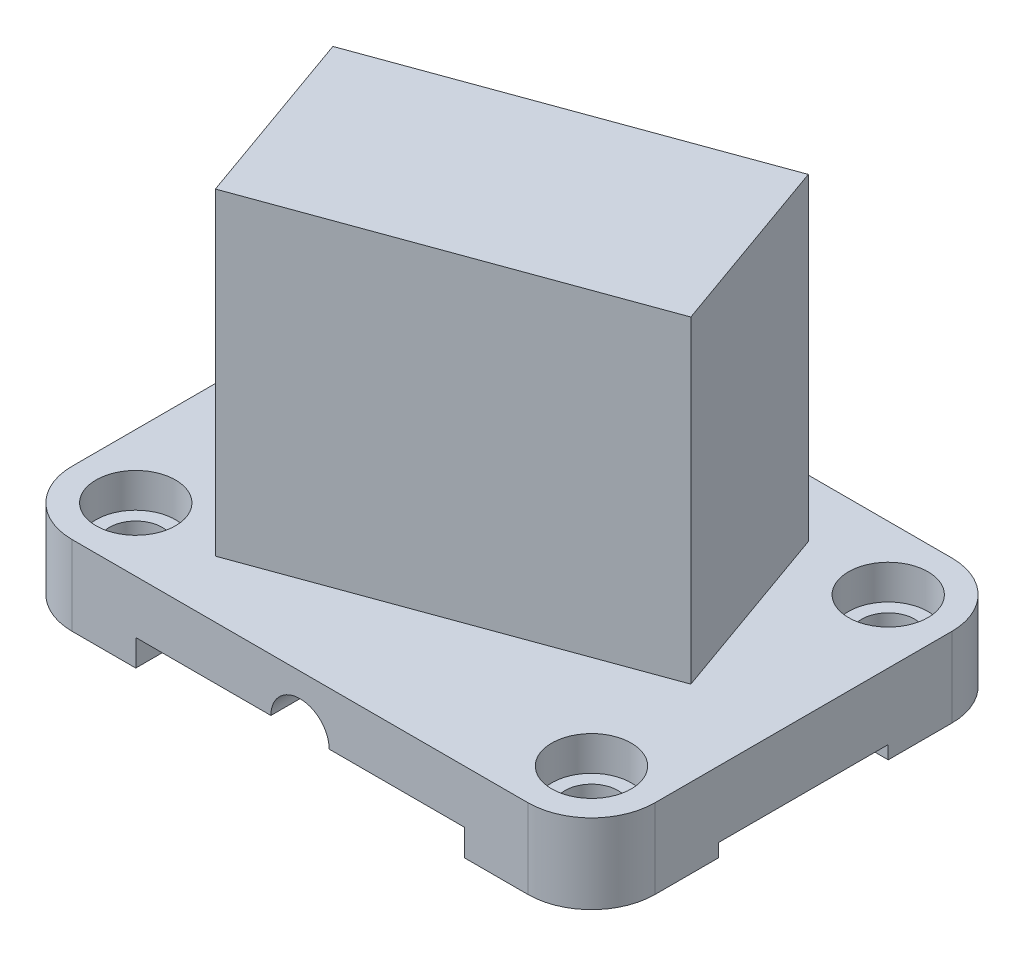
SolidWorks part; units mm, degrees
ref_plane "Front Plane" through (0, 0, 0) normal (0, 0, 1) x (1, 0, 0)
ref_plane "Top Plane" through (0, 0, 0) normal (0, 1, 0) x (1, 0, 0)
ref_plane "Right Plane" through (0, 0, 0) normal (1, 0, 0) x (0, 0, -1)
sketch "Sketch1" plane through (0, 0, 0) normal (0, 1, 0) x (1, 0, 0)
  line L1 (-54.61, 50.8) -> (54.61, 50.8)
  line L2 (-69.85, 35.56) -> (-69.85, -35.56)
  line L3 (-54.61, -50.8) -> (54.61, -50.8)
  line L4 (69.85, 35.56) -> (69.85, -35.56)
  line L5 (-69.85, 50.8) -> (69.85, -50.8) construction
  line L6 (-69.85, -50.8) -> (69.85, 50.8) construction
  arc A0 (-54.61, 50.8) -> (-69.85, 35.56) centre (-54.61, 35.56) ccw
  arc A1 (54.61, 50.8) -> (69.85, 35.56) centre (54.61, 35.56) cw
  arc A2 (54.61, -50.8) -> (69.85, -35.56) centre (54.61, -35.56) ccw
  arc A3 (-69.85, -35.56) -> (-54.61, -50.8) centre (-54.61, -35.56) ccw
  point P0 (0, 0)
  dimension "D3" = 15.24
  dimension "D1" = 139.7
  dimension "D2" = 101.6
extrude "Boss-Extrude1" add sketch "Sketch1" along normal blind 19.05
sketch "Sketch2" plane through (0, 19.05, 0) normal (0, 1, 0) x (1, 0, 0)
  point P0 (-54.61, 35.56)
  point P1 (54.61, 35.56)
  point P3 (-54.61, -35.56)
  point P5 (54.61, -35.56)
hole_wizard "CBORE for 1/2 Hex Head Bolt1" positions "Sketch2" profile "Sketch3" counterbore size "1/2" standard "ANSI Inch" end condition up to next
sketch "Sketch3" plane through (-54.61, 19.05, -35.56) normal (1, 0, 0) x (0, 0, 1)
  line L0 (0, 0) -> (0, 19.05)
  line L1 (0, 19.05) -> (6.35, 19.05)
  line L3 (6.35, 19.05) -> (6.35, 8.255)
  line L4 (6.35, 8.255) -> (9.525, 8.255)
  line L5 (9.525, 8.255) -> (9.525, 0)
  line L7 (9.525, 0) -> (0, 0)
  line L11 (0, -6.35) -> (0, 107.95) construction
  dimension "Thru Hole Dia." = 12.7
  dimension "Thru Hole Depth" = 19.05
  dimension "C'Bore Dia." = 19.05
  dimension "C'Bore Depth" = 8.255
sketch "Sketch4" plane through (0, 0, 50.8) normal (0, 0, 1) x (1, 0, 0)
  line L0 (-39.37, 0) -> (-39.37, 6.35)
  line L1 (-54.61, 0) -> (54.61, 0) construction
  line L2 (-39.37, 6.35) -> (-6.985, 6.35)
  line L3 (39.37, 6.35) -> (39.37, 0)
  line L4 (39.37, 0) -> (-39.37, 0)
  line L5 (-69.85, 19.05) -> (-69.85, 0) construction
  line L6 (6.985, 6.35) -> (39.37, 6.35)
  arc A0 (6.985, 6.35) -> (-6.985, 6.35) centre (0, 6.35) ccw
  dimension "D4" = 13.97
  dimension "D1" = 6.35
  dimension "D2" = 39.37
  dimension "D3" = 30.48
extrude "Cut-Extrude1" cut sketch "Sketch4" against normal through all
sketch "Sketch5" plane through (-69.85, 0, 0) normal (-1, 0, 0) x (0, 0, 1)
  line L0 (-20.32, 0) -> (-20.32, 3.175)
  line L1 (-35.56, 0) -> (35.56, 0) construction
  line L2 (-20.32, 3.175) -> (20.32, 3.175)
  line L3 (20.32, 3.175) -> (20.32, 0)
  line L4 (20.32, 0) -> (-20.32, 0)
  line L5 (-50.8, 19.05) -> (-50.8, 0) construction
  line L6 (50.8, 19.05) -> (50.8, 0) construction
  dimension "D1" = 30.48
  dimension "D2" = 30.48
  dimension "D3" = 3.175
extrude "Cut-Extrude2" cut sketch "Sketch5" against normal through all
sketch "Sketch6" plane through (0, 19.05, 0) normal (0, 1, 0) x (1, 0, 0)
  line L0 (-49.53, 6.604) -> (-34.0087, -37.0752)
  line L1 (-34.0087, -37.0752) -> (49.53, -6.6696)
  line L2 (49.53, -6.6696) -> (34.0087, 37.0096)
  line L3 (34.0087, 37.0096) -> (-49.53, 6.604)
  line L4 (-54.61, -50.8) -> (54.61, -50.8) construction
  line L5 (-69.85, 35.56) -> (-69.85, -35.56) construction
  line L6 (69.85, -35.56) -> (69.85, 35.56) construction
  dimension "D1" = 20
  dimension "D2" = 20.32
  dimension "D3" = 57.404
  dimension "D4" = 46.355
  dimension "D5" = 88.9
  dimension "D6" = 20.32
extrude "Boss-Extrude2" add sketch "Sketch6" along normal blind 76.2
